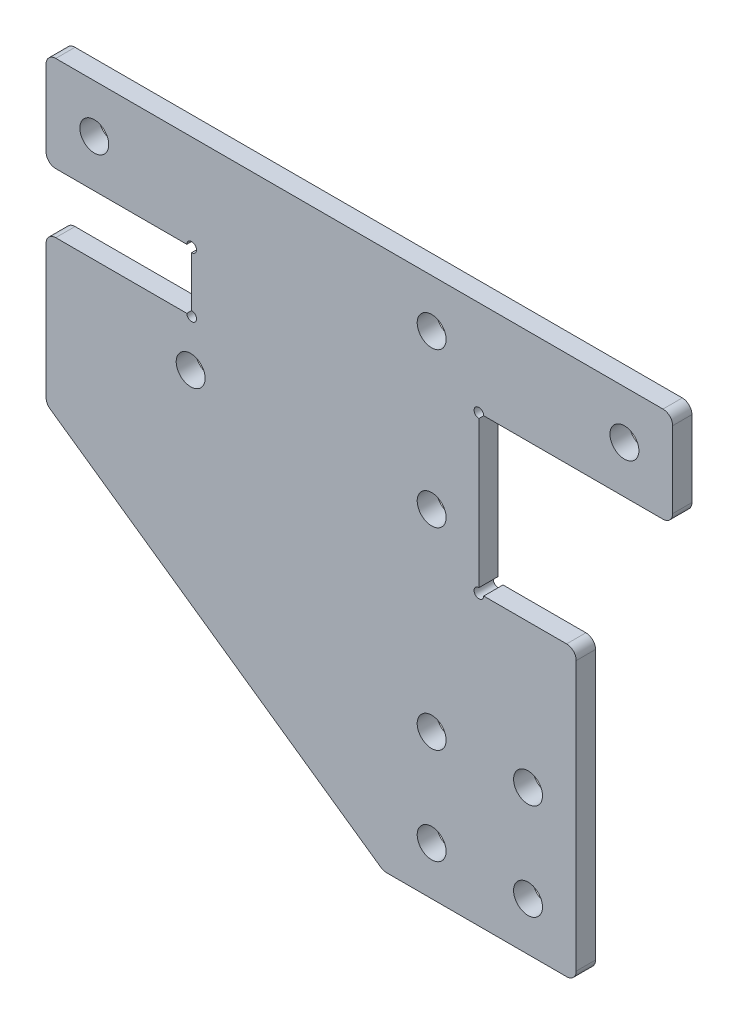
SolidWorks part; units mm, degrees
material "环氧板3240"
ref_plane "前视基准面" through (0, 0, 0) normal (0, 0, 1) x (1, 0, 0)
ref_plane "上视基准面" through (0, 0, 0) normal (0, 1, 0) x (1, 0, 0)
ref_plane "右视基准面" through (0, 0, 0) normal (1, 0, 0) x (0, 0, -1)
other "Configuration Table"
sketch "草图1" plane through (0, 0, 0) normal (0, 0, 1) x (1, 0, 0)
  line L2 (15, -35) -> (15, -5.1)
  line L6 (-40, 16) -> (25, 16) construction
  line L7 (10, -5.1) -> (10, -35) construction
  line L10 (15, -5.1) -> (4.9, -5.1)
  line L11 (4.9, -5.1) -> (4.9, 11.1)
  line L13 (-40, -10.4927) -> (-5, -35)
  line L17 (4.9, 11.1) -> (25, 11.1)
  line L18 (-24.9, 4.9) -> (-40, 4.9)
  line L20 (-40, 11.1) -> (-24.9, 11.1)
  line L21 (-24.9, 11.1) -> (-24.9, 4.9)
  line L22 (-40, 21) -> (25, 21)
  line L23 (25, 21) -> (25, 11.1)
  line L29 (-40, 21) -> (-40, 11.1)
  line L31 (15, -35) -> (-5, -35)
  line L32 (-40, 4.9) -> (-40, -10.4927)
  line L33 (-40, 0) -> (4.9, 0) construction
  line L34 (0, 0) -> (0, -35) construction
  line L35 (0, -20) -> (10, -20) construction
  line L36 (0, -30) -> (10, -30) construction
  circle A1 centre (-35, 16) radius 1.5
  circle A2 centre (10, -30) radius 1.5
  circle A3 centre (10, -20) radius 1.5
  circle A4 centre (0, 16) radius 1.5
  circle A6 centre (20, 16) radius 1.5
  circle A7 centre (-25, 0) radius 1.5
  circle A8 centre (0, 0) radius 1.5
  circle A9 centre (0, -20) radius 1.5
  circle A10 centre (0, -30) radius 1.5
  dimension "D7" = 10
  dimension "D8" = 10.1
  dimension "D9" = 35
  dimension "D10" = 16.2
  dimension "D11" = 10
  dimension "D6" = 5
  dimension "D4" = 20
  dimension "D15" = 5
  dimension "D20" = 10
  dimension "D22" = 65
  dimension "D13" = 20
  dimension "D12" = 3
  dimension "D24" = 25
  dimension "D19" = 15.6988
  dimension "D3" = 16
  dimension "D5" = 5
  dimension "D14" = 35
  dimension "D16" = 20
  dimension "D17" = 6.2
  dimension "D18" = 35
  dimension "D21" = 4.9
  dimension "D26" = 39.9
extrude "凸台-拉伸1" add sketch "草图1" along normal blind 2
sketch "草图2" plane through (0, 0, 0) normal (0, 0, -1) x (-1, 0, 0)
  circle A0 centre (-4.9, 11.1) radius 0.5
  circle A1 centre (-4.9, -5.1) radius 0.5
  circle A2 centre (24.9, 11.1) radius 0.5
  circle A3 centre (24.9, 4.9) radius 0.5
  dimension "D1" = 1
extrude "切除-拉伸1" cut sketch "草图2" against normal blind 10
fillet "圆角2" radius 1 9 edges at (-5, -35, 1) (15, -35, 1) (15, -5.1, 1) (25, 11.1, 1) (25, 21, 1) (-40, 21, 1) (-40, 11.1, 1) (-40, -10.4927, 1) (-40, 4.9, 1)
